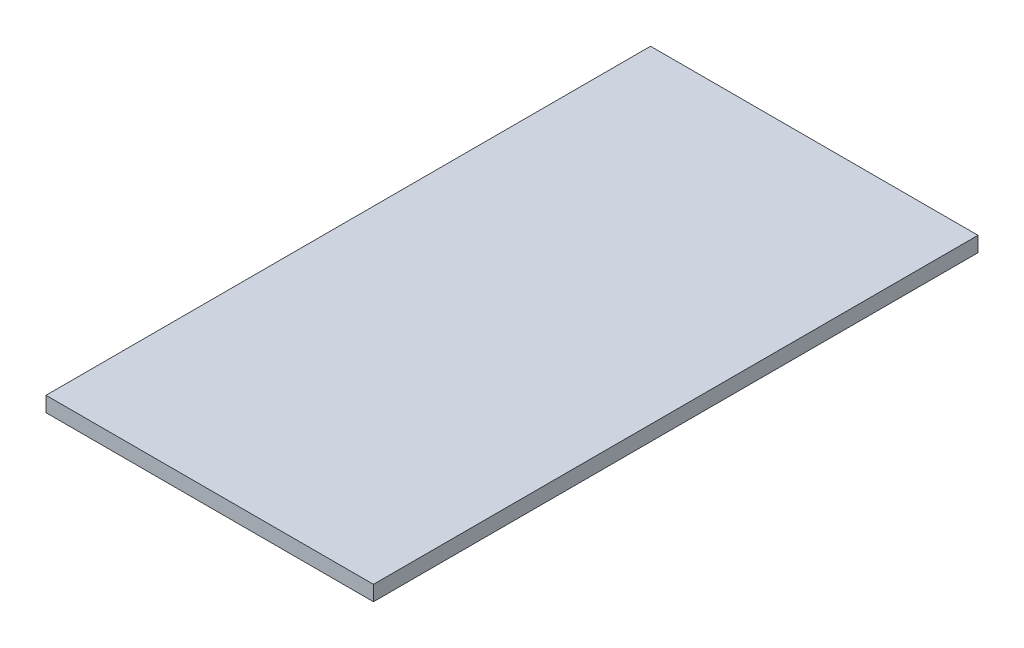
SolidWorks part; units mm, degrees
ref_plane "Front Plane" through (0, 0, 0) normal (0, 0, 1) x (1, 0, 0)
ref_plane "Top Plane" through (0, 0, 0) normal (0, 1, 0) x (1, 0, 0)
ref_plane "Right Plane" through (0, 0, 0) normal (1, 0, 0) x (0, 0, -1)
sketch "Sketch1" plane through (0, 0, 0) normal (0, 1, 0) x (1, 0, 0)
  line L1 (-76.9872, 66.2643) -> (-11.9872, 66.2643)
  line L2 (-76.9872, 66.2643) -> (-76.9872, -53.7357)
  line L3 (-76.9872, -53.7357) -> (-11.9872, -53.7357)
  line L4 (-11.9872, 66.2643) -> (-11.9872, -53.7357)
  dimension "D1" = 120
  dimension "D2" = 65
extrude "Boss-Extrude1" add sketch "Sketch1" along normal blind 2
sketch "Sketch2" plane through (0, 2, 0) normal (0, 1, 0) x (1, 0, 0)
  line L1 (-76.9872, 66.2643) -> (-11.9872, 66.2643)
  line L2 (-76.9872, 66.2643) -> (-76.9872, -53.7357)
  line L3 (-76.9872, -53.7357) -> (-11.9872, -53.7357)
  line L4 (-11.9872, 66.2643) -> (-11.9872, -53.7357)
extrude "Boss-Extrude3" add sketch "Sketch2" along normal blind 1
